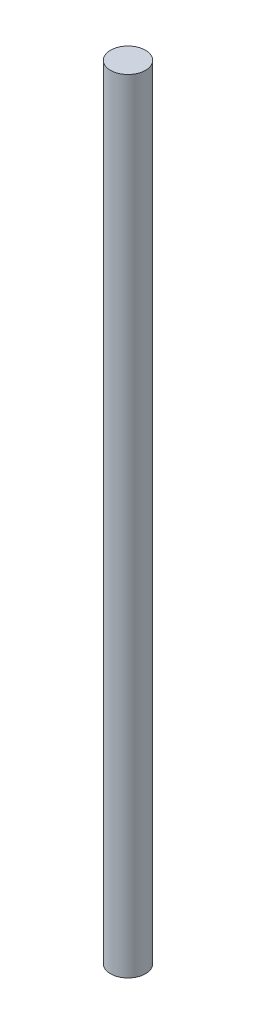
SolidWorks part; units mm, degrees
ref_plane "Front Plane" through (0, 0, 0) normal (0, 0, 1) x (1, 0, 0)
ref_plane "Top Plane" through (0, 0, 0) normal (0, 1, 0) x (1, 0, 0)
ref_plane "Right Plane" through (0, 0, 0) normal (1, 0, 0) x (0, 0, -1)
sketch "Sketch1" plane through (0, 0, 0) normal (0, 1, 0) x (1, 0, 0)
  circle A0 centre (0, 0) radius 3.9688
  dimension "D1" = 7.9375
extrude "Boss-Extrude1" add sketch "Sketch1" along normal blind 177.8
